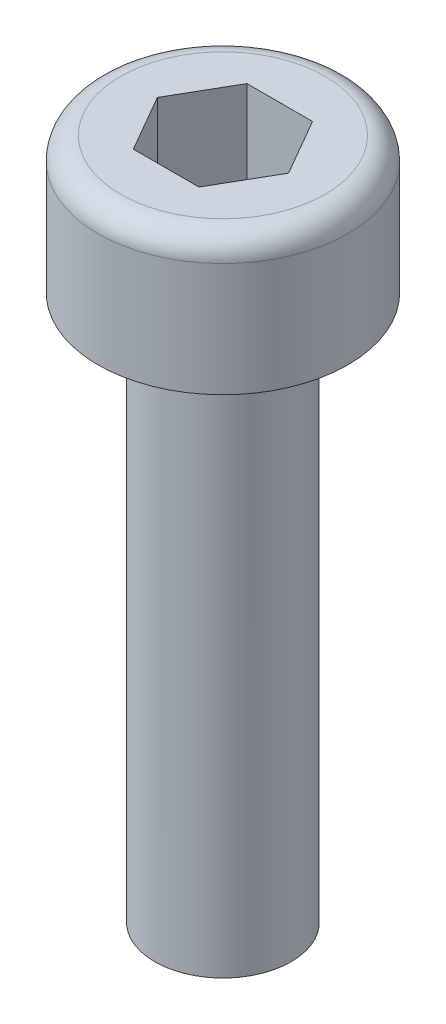
SolidWorks part; units mm, degrees
material "Alloy Steel"
ref_plane "Plane1" through (0, 0, 0) normal (0, 0, 1) x (1, 0, 0)
ref_plane "Plane2" through (0, 0, 0) normal (0, 1, 0) x (1, 0, 0)
ref_plane "Plane3" through (0, 0, 0) normal (1, 0, 0) x (0, 0, -1)
sketch "Sketch1" plane through (0, 0, 0) normal (0, 0, 1) x (1, 0, 0)
  line L0 (0, -12.4019) -> (0, 3)
  line L1 (0, 3) -> (2.25, 3)
  line L2 (2.75, 2.5) -> (2.75, 0)
  line L3 (2.75, 0) -> (1.5, 0)
  line L4 (1.5, 0) -> (1.5, -12)
  line L5 (1.5, -12) -> (0, -12.4019)
  line L6 (0, 3) -> (0, 17) construction
  arc A0 (2.25, 3) -> (2.75, 2.5) centre (2.25, 2.5) cw
  point P10 (2.75, 3)
  dimension "D6" = 0.5
  dimension "D1" = 2.75
  dimension "D2" = 3
  dimension "D3" = 1.5
  dimension "D4" = 12
  dimension "D5" = 75
revolve "Base-Revolve" add sketch "Sketch1" angle 360 about L6
sketch "Sketch2" plane through (0, 3, 0) normal (0, 1, 0) x (-1, 0, 0)
  line L1 (-1.4434, 0) -> (-0.7217, -1.25)
  line L2 (-0.7217, -1.25) -> (0.7217, -1.25)
  line L3 (0.7217, -1.25) -> (1.4434, 0)
  line L4 (1.4434, 0) -> (0.7217, 1.25)
  line L5 (0.7217, 1.25) -> (-0.7217, 1.25)
  line L6 (-0.7217, 1.25) -> (-1.4434, 0)
  circle A0 centre (0, 0) radius 1.25 construction
  dimension "D1" = 2.5
extrude "Cut-Extrude1" cut sketch "Sketch2" against normal blind 2
